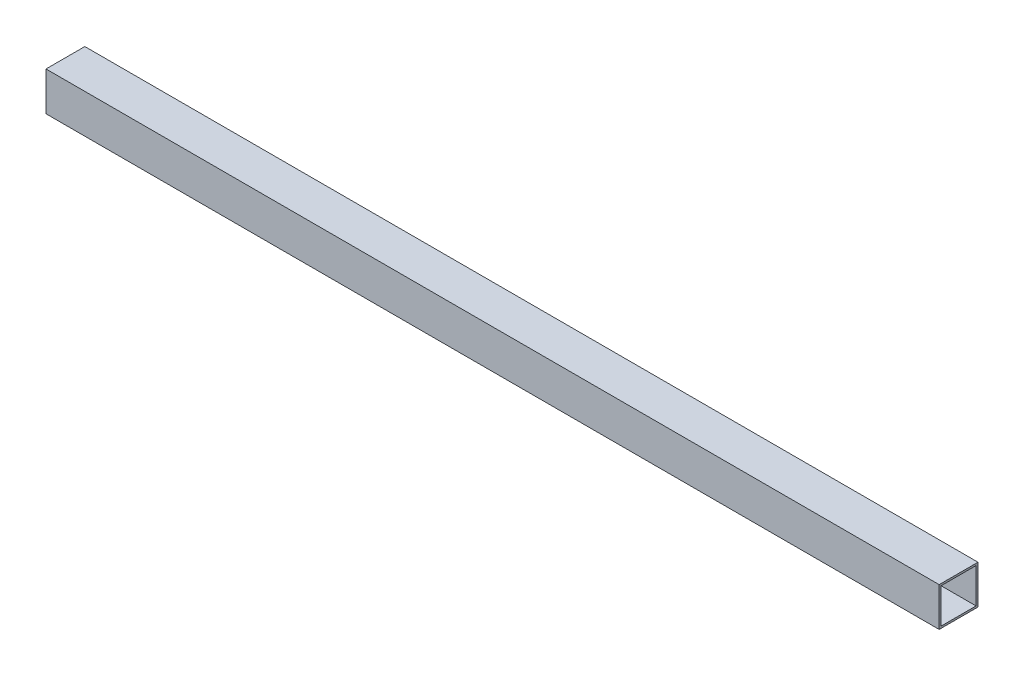
SolidWorks part; units mm, degrees
ref_plane "Alzado" through (0, 0, 0) normal (0, 0, 1) x (1, 0, 0)
ref_plane "Planta" through (0, 0, 0) normal (0, 1, 0) x (1, 0, 0)
ref_plane "Vista lateral" through (0, 0, 0) normal (1, 0, 0) x (0, 0, -1)
sketch "Croquis1" plane through (0, 0, 0) normal (1, 0, 0) x (0, 0, -1)
  line L1 (-20, -20) -> (20, -20)
  line L2 (-20, -20) -> (-20, 20)
  line L3 (-20, 20) -> (20, 20)
  line L4 (20, -20) -> (20, 20)
  line L5 (-20, -20) -> (20, 20) construction
  line L6 (-20, 20) -> (20, -20) construction
  line L7 (-18, -18) -> (18, -18)
  line L8 (-18, -18) -> (-18, 18)
  line L9 (-18, 18) -> (18, 18)
  line L10 (18, -18) -> (18, 18)
  line L11 (-18, -18) -> (18, 18) construction
  line L12 (-18, 18) -> (18, -18) construction
  point P0 (0, 0)
  point P6 (0, 0)
  dimension "D1" = 2
  dimension "D2" = 40
  dimension "D3" = 2
extrude "Saliente-Extruir1" add sketch "Croquis1" along normal blind 920
